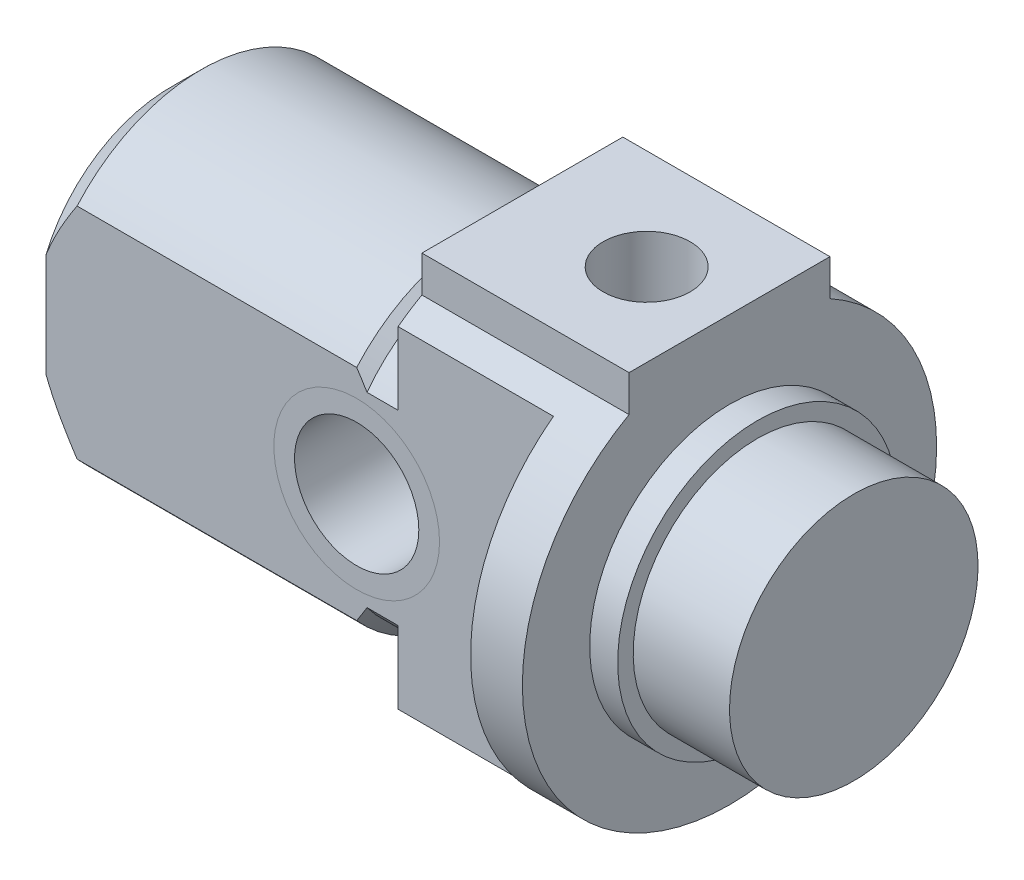
SolidWorks part; units mm, degrees
material "6061-T6 (SS)"
ref_plane "Front Plane" through (0, 0, 0) normal (0, 0, 1) x (1, 0, 0)
ref_plane "Top Plane" through (0, 0, 0) normal (0, 1, 0) x (1, 0, 0)
ref_plane "Right Plane" through (0, 0, 0) normal (1, 0, 0) x (0, 0, -1)
sketch "Sketch1" plane through (0, 0, 0) normal (1, 0, 0) x (0, 0, -1)
  line L0 (0, 0) -> (0, 17.9915) construction
  line L1 (-4.85, 8.7451) -> (-4.85, 10.5)
  line L2 (4.85, 8.7451) -> (4.85, 10.5)
  line L6 (-4.85, 10.5) -> (4.85, 10.5)
  arc A0 (-4.85, 8.7451) -> (4.85, 8.7451) centre (0, 0) ccw
  dimension "RM DIAD2" = 20
  dimension "RMD1" = 9.7
  dimension "RM HEOGHT D3" = 20.5
extrude "Boss-Extrude1" add sketch "Sketch1" along normal blind 33
sketch "Sketch2" plane through (0, 0, 0) normal (0, 0, 1) x (1, 0, 0)
  line L0 (27, 14) -> (27, 6.75)
  line L1 (27, 6.75) -> (28.35, 6.75)
  line L2 (28.35, 6.75) -> (28.35, 6)
  line L3 (28.35, 6) -> (33, 6)
  line L4 (33, -10) -> (33, 8.7451) construction
  line L5 (33, 6) -> (33, 14)
  line L6 (33, 0) -> (0, 0) construction
  line L7 (27, 14) -> (33, 14)
  line L8 (45.5, 0) -> (0, 0) construction
  dimension "BARREL STEP D1" = 13.5
  dimension "BARREL DIA D2" = 12
  dimension "BARREL GUIDED3" = 4.65
  dimension "BARREL EXTRA D4" = 6
  dimension "BARREL SUMA D5" = 8
revolve "Cut-Revolve1" cut sketch "Sketch2" angle 360 about L8
sketch "Sketch3" plane through (0, 0, 0) normal (0, 0, 1) x (1, 0, 0)
  line L0 (0, 0) -> (15.0791, 0) construction
  line L1 (0, 8.7451) -> (0, -10) construction
  line L2 (0, 8) -> (15, 8)
  line L3 (15, 8) -> (15.5, 7.5)
  line L4 (0, 8) -> (0, 16)
  line L5 (0, 16) -> (17, 16)
  line L6 (15.5, 7.5) -> (17, 7.5)
  line L7 (17, 7.5) -> (17, 16)
  line L10 (27, 0) -> (0, 0) construction
  dimension "THREAD SUMA D1" = 8
  dimension "THREAD DIA D2" = 16
  dimension "THREAD LENGTH D3" = 17
  dimension "THREAD ANGLED4" = 45
  dimension "THREAD GROOVE WIDTHD5" = 1.5
  dimension "THREAD GROOVE DIAD6" = 15
revolve "Cut-Revolve2" cut sketch "Sketch3" angle 360 about L0
cosmetic thread "Cosmetic Thread1" parameters "THREAD SIZE D2"=10.619
chamfer "Chamfer1" distance 1.5 angle 45 1 edges at (0, 0, 8)
hole_wizard "G1/8 Tapped Hole1" positions "Sketch5" profile "Sketch4" tap size "G1/8" standard "BSI"
sketch "Sketch5" plane through (0, 10.5, 0) normal (0, 1, 0) x (-1, 0, 0)
  line L0 (-28.35, 6.75) -> (-28.35, -6.75) construction
  line L6 (-15, 0) -> (-1.5, 0) construction
  point P0 (-23, 0)
  dimension "HOLE LOCATION D1" = 5.35
sketch "Sketch4" plane through (23, 10.5, 0) normal (1, 0, 0) x (0, 0, 1)
  line L0 (0, 0) -> (0, 12.2618)
  line L1 (0, 12.2618) -> (2.1, 11)
  line L2 (2.1, 11) -> (2.1, 0)
  line L5 (2.1, 0) -> (0, 0)
  line L10 (0, 12.2618) -> (-2.1, 11) construction
  line L11 (0, -6.35) -> (0, 107.95) construction
  dimension "Tap Drill Dia." = 4.2
  dimension "Tap Drill Depth" = 11
  dimension "Drill Angle" = 118
cosmetic thread "Hole Thread1" parameters "D1"=11, "D2"=5
sketch "Sketch6" plane through (33, 0, 0) normal (1, 0, 0) x (0, 0, -1)
  circle A0 centre (0, 0) radius 3
  dimension "PISTON ROD SIZE D1" = 6
extrude "Cut-Extrude1" [suppressed] cut sketch "Sketch6" against normal through all
sketch "Sketch7" plane through (28.35, 0, 0) normal (1, 0, 0) x (0, 0, -1)
  line L0 (-6, 8) -> (-6, -8)
  line L1 (-6, -8) -> (-21, -8)
  line L2 (-21, -8) -> (-21, 8)
  line L3 (-21, 8) -> (-6, 8)
  line L5 (0, -0.5) -> (0, 10.5) construction
  arc A0 (-4.85, 8.7451) -> (4.85, 8.7451) centre (0, 0) ccw construction
  dimension "D1" = 15
  dimension "SLOT D1" = 6
extrude "Cut-Extrude2" cut sketch "Sketch7" against normal through all from offset 3.85 offset against normal yes
mirror "Mirror1" about plane through (0, 0, 0) normal (0, 0, 1) of "Cut-Extrude2"
sketch "Sketch8" plane through (0, 0, 6) normal (0, 0, 1) x (1, 0, 0)
  line L0 (15, 0) -> (15.5, 0) construction
  line L1 (17, 0) -> (15.5, 0) construction
  line L2 (28.35, -6.75) -> (28.35, 6.75) construction
  circle A0 centre (15, 0) radius 4
  dimension "HOLE D1" = 8
  dimension "HOLE DIST D2" = 13.35
extrude "Cut-Extrude3" cut sketch "Sketch8" against normal through all
sketch "Sketch9" plane through (27, 0, 0) normal (1, 0, 0) x (0, 0, -1)
  line L0 (-4.3116, 7.9) -> (4.3116, 7.9)
  line L1 (-4.3116, -7.9) -> (4.3116, -7.9)
  line L2 (7.9, 4.3116) -> (7.9, -4.3116)
  line L3 (-7.9, 4.3116) -> (-7.9, -4.3116)
  line L4 (0, 0) -> (0, 7.9) construction
  line L5 (0, -0.5) -> (0, 10.5) construction
  line L6 (0, 0) -> (7.9, 0) construction
  line L7 (0, 9) -> (0, 10.5876) construction
  line L8 (9, 0) -> (10, 0) construction
  line L10 (-12.5, 12.5) -> (12.5, 12.5)
  line L11 (-12.5, 12.5) -> (-12.5, -12.5)
  line L12 (-12.5, -12.5) -> (12.5, -12.5)
  line L13 (12.5, 12.5) -> (12.5, -12.5)
  line L14 (-12.5, 12.5) -> (12.5, -12.5) construction
  line L15 (-12.5, -12.5) -> (12.5, 12.5) construction
  arc A0 (-4.3116, 7.9) -> (-7.9, 4.3116) centre (0, 0) ccw
  arc A1 (-4.85, 8.7451) -> (4.85, 8.7451) centre (0, 0) ccw construction
  arc A2 (7.9, 4.3116) -> (4.3116, 7.9) centre (0, 0) ccw
  arc A3 (4.3116, -7.9) -> (7.9, -4.3116) centre (0, 0) ccw
  arc A4 (-7.9, -4.3116) -> (-4.3116, -7.9) centre (0, 0) ccw
  dimension "D1" = 18
  dimension "D2" = 15.8
  dimension "D3" = 15.8
  dimension "D4" = 25
  dimension "D5" = 25
extrude "Cut-Extrude4" [suppressed] cut sketch "Sketch9" against normal through all
sketch "Sketch11" plane through (0, 0, 6) normal (0, 0, 1) x (1, 0, 0)
  circle A0 centre (15, 0) radius 4 construction
  circle A1 centre (15, 0) radius 4
  circle A2 centre (15, 0) radius 3
  dimension "D1" = 6
extrude "Boss-Extrude2" add sketch "Sketch11" against normal up to surface (12 mm away) separate body up to face at (11, 0, -6)
sketch "Sketch12" plane through (0, 0, 0) normal (-1, 0, 0) x (0, 0, 1)
  line L0 (-4.85, 8.7451) -> (-4.85, 10.5)
  line L1 (-4.85, 10.5) -> (4.85, 10.5)
  line L2 (4.85, 10.5) -> (4.85, 8.7451)
  arc A0 (-4.85, 8.7451) -> (4.85, 8.7451) centre (0, 0) ccw
